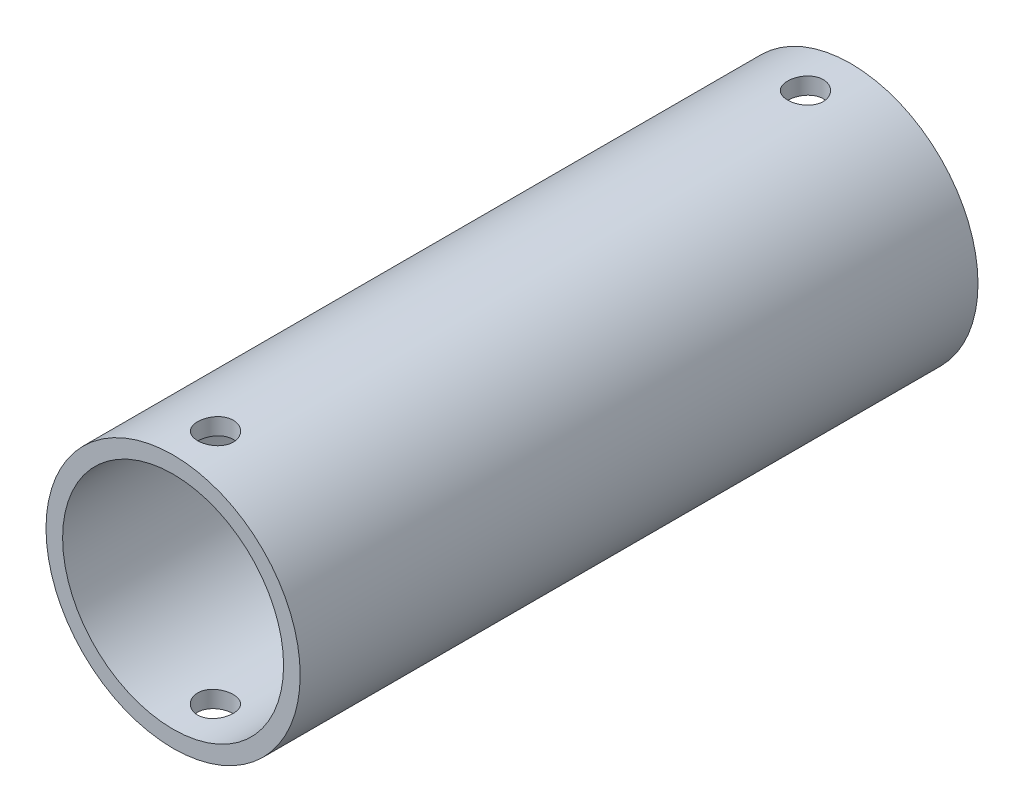
SolidWorks part; units mm, degrees
material "6061-T6 (SS)"
ref_plane "Front" through (0, 0, 0) normal (0, 0, 1) x (1, 0, 0)
ref_plane "Top" through (0, 0, 0) normal (0, 1, 0) x (1, 0, 0)
ref_plane "Right" through (0, 0, 0) normal (1, 0, 0) x (0, 0, -1)
sketch "Sketch1" plane through (0, 0, 0) normal (0, 0, 1) x (1, 0, 0)
  circle A0 centre (0, 0) radius 9.525
  circle A1 centre (0, 0) radius 8.2804
  dimension "D1" = 19.05
  dimension "D2" = 1.2446
extrude "Boss-Extrude1" add sketch "Sketch1" along normal blind 50.8
sketch "Sketch2" plane through (0, 0, 0) normal (0, 1, 0) x (1, 0, 0)
  line L0 (-9.525, -50.8) -> (9.525, -50.8) construction
  line L1 (-9.525, -50.8) -> (9.525, -50.8) construction
  line L2 (0, -47.625) -> (0, -50.8) construction
  line L3 (9.525, 0) -> (-9.525, 0) construction
  line L4 (9.525, 0) -> (-9.525, 0) construction
  line L5 (0, 0) -> (0, -51.0326) construction
  line L6 (0, -25.5163) -> (5.8163, -25.5163) construction
  circle A0 centre (0, -47.625) radius 1.3335
  circle A1 centre (0, -3.4076) radius 1.3335
  dimension "D1" = 3.175
  dimension "D2" = 2.667
extrude "Cut-Extrude1" cut sketch "Sketch2" against normal through all and the other way through all
